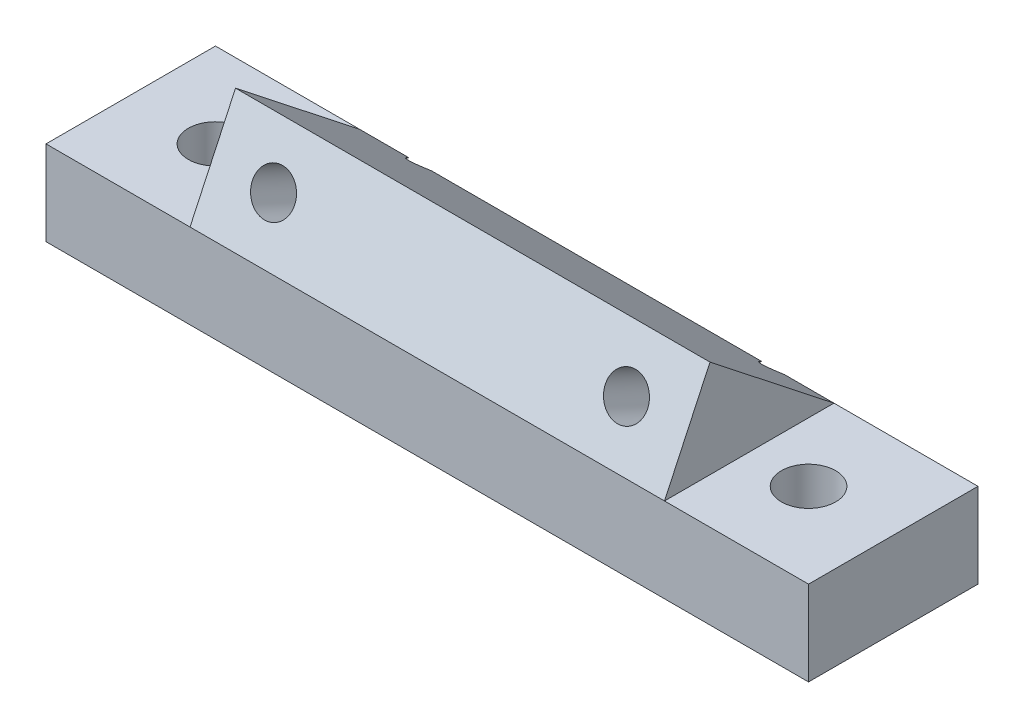
SolidWorks part; units mm, degrees
ref_plane "Front Plane" through (0, 0, 0) normal (0, 0, 1) x (1, 0, 0)
ref_plane "Top Plane" through (0, 0, 0) normal (0, 1, 0) x (1, 0, 0)
ref_plane "Right Plane" through (0, 0, 0) normal (1, 0, 0) x (0, 0, -1)
sketch "Sketch1" plane through (0, 0, 0) normal (0, 1, 0) x (1, 0, 0)
  line L0 (-22.5, 0) -> (22.5, 0) construction
  line L1 (-22.5, 5) -> (22.5, 5)
  line L2 (-22.5, 5) -> (-22.5, -5)
  line L3 (-22.5, -5) -> (22.5, -5)
  line L4 (22.5, 5) -> (22.5, -5)
  line L5 (-22.5, 5) -> (22.5, -5) construction
  line L6 (-22.5, -5) -> (22.5, 5) construction
  line L7 (0, -5) -> (0, 5) construction
  circle A0 centre (-17.5, 0) radius 1.6
  circle A1 centre (17.5, 0) radius 1.6
  point P0 (0, 0)
  dimension "D2" = 3.2
  dimension "D3" = 17.5
  dimension "D1" = 45
  dimension "D4" = 10
extrude "Boss-Extrude2" add sketch "Sketch1" along normal blind 5
sketch "Sketch3" plane through (0, 0, 0) normal (1, 0, 0) x (0, 0, -1)
  line L0 (-5, 5) -> (5, 5) construction
  line L1 (-5, 5) -> (5, 5)
  line L2 (-5, 5) -> (-2.3164, 10.7551)
  line L3 (-2.3164, 10.7551) -> (5, 5)
  dimension "D1" = 65
  dimension "D2" = 6.35
extrude "Boss-Extrude3" add sketch "Sketch3" along normal mid plane 28
sketch "Sketch4" plane through (0, 2.8081, 6.0221) normal (0, 0.4226, 0.9063) x (1, 0, 0)
  line L0 (-14, 5.5934) -> (14, 5.5934) construction
  line L1 (-14, 8.7684) -> (-14, 2.4184) construction
  line L2 (14, 8.7684) -> (14, 2.4184) construction
  line L3 (0, 2.4184) -> (0, 8.7684) construction
  line L4 (14, 2.4184) -> (-14, 2.4184) construction
  line L5 (14, 8.7684) -> (-14, 8.7684) construction
  circle A0 centre (-10.414, 5.5934) radius 1.25
  circle A1 centre (10.414, 5.5934) radius 1.25
  dimension "D1" = 2.5
  dimension "D2" = 10.414
extrude "Cut-Extrude1" cut sketch "Sketch4" against normal blind 28
